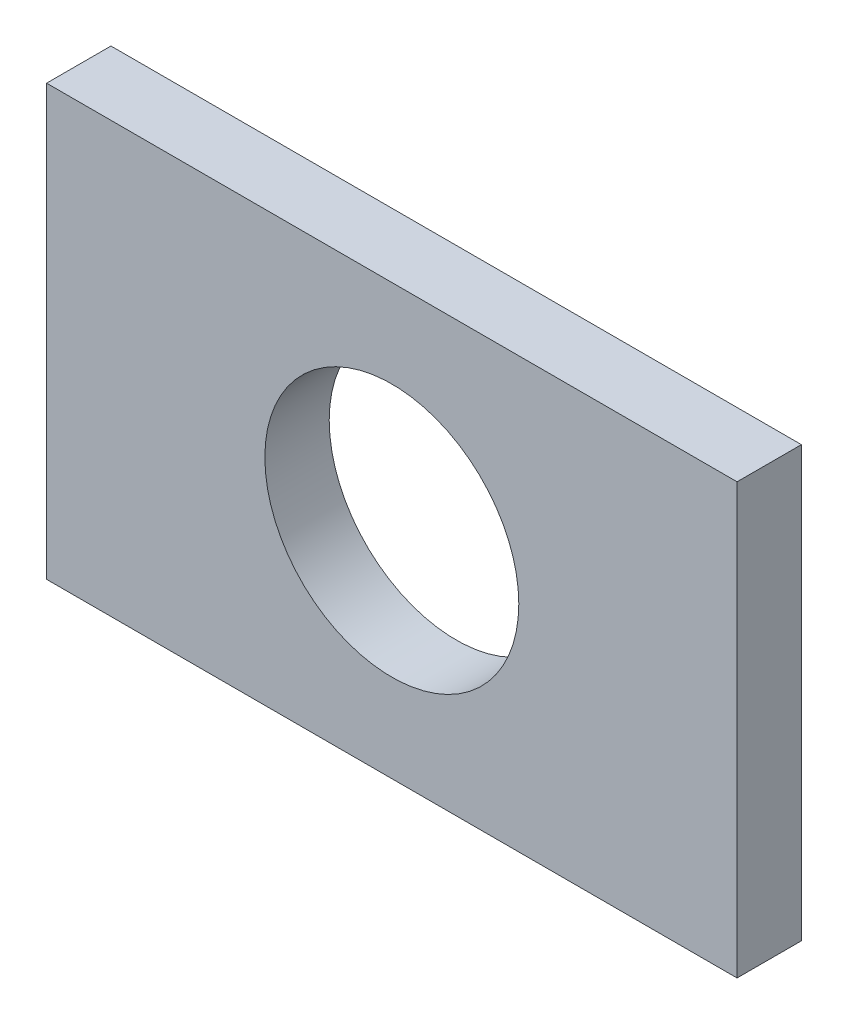
SolidWorks part; units mm, degrees
ref_plane "Plan de face" through (0, 0, 0) normal (0, 0, 1) x (1, 0, 0)
ref_plane "Plan de dessus" through (0, 0, 0) normal (0, 1, 0) x (1, 0, 0)
ref_plane "Plan de droite" through (0, 0, 0) normal (1, 0, 0) x (0, 0, -1)
sketch "Esquisse1" plane through (0, 0, 0) normal (0, 0, 1) x (1, 0, 0)
  line L1 (-53.647, 33.3892) -> (53.647, 33.3892)
  line L2 (-53.647, 33.3892) -> (-53.647, -33.3892)
  line L3 (-53.647, -33.3892) -> (53.647, -33.3892)
  line L4 (53.647, 33.3892) -> (53.647, -33.3892)
  line L5 (-53.647, 33.3892) -> (53.647, -33.3892) construction
  line L6 (-53.647, -33.3892) -> (53.647, 33.3892) construction
  point P0 (0, 0)
extrude "Boss.-Extru.1" add sketch "Esquisse1" along normal blind 10
sketch "Esquisse2" plane through (0, 0, 10) normal (0, 0, 1) x (1, 0, 0)
  circle A0 centre (0, 0) radius 19.7318
extrude "Enlèv. mat.-Extru.1" cut sketch "Esquisse2" against normal blind 10
